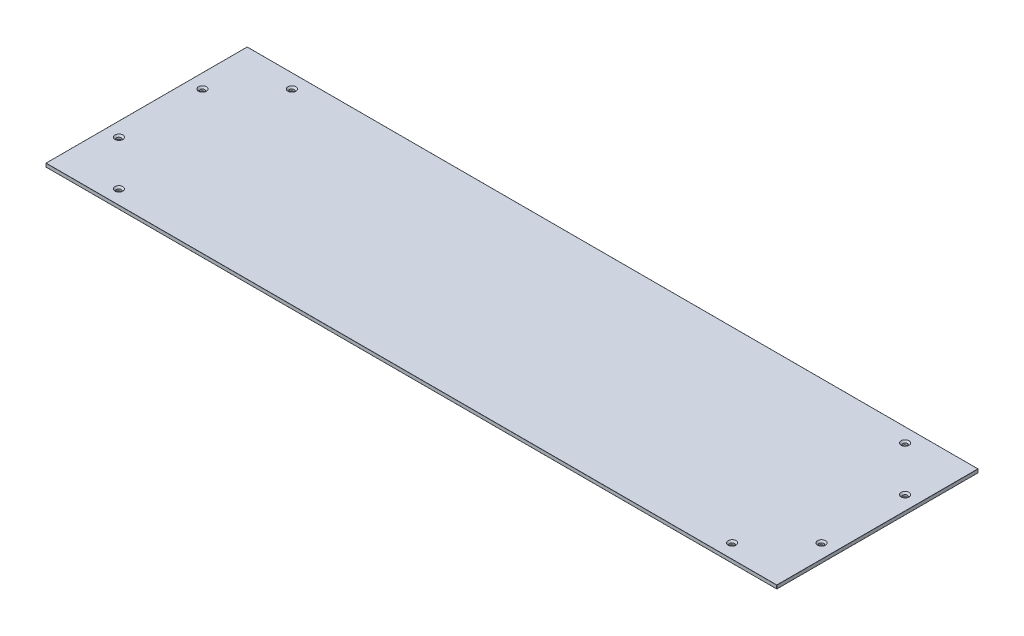
SolidWorks part; units mm, degrees
material "Glass"
ref_plane "Front Plane" through (0, 0, 0) normal (0, 0, 1) x (1, 0, 0)
ref_plane "Top Plane" through (0, 0, 0) normal (0, 1, 0) x (1, 0, 0)
ref_plane "Right Plane" through (0, 0, 0) normal (1, 0, 0) x (0, 0, -1)
sketch "Sketch1" plane through (0, 0, 0) normal (0, 1, 0) x (1, 0, 0)
  line L1 (-621, 171) -> (621, 171)
  line L2 (-621, 171) -> (-621, -171)
  line L3 (-621, -171) -> (621, -171)
  line L4 (621, 171) -> (621, -171)
  line L5 (-621, 171) -> (621, -171) construction
  line L6 (-621, -171) -> (621, 171) construction
  point P0 (0, 0)
  dimension "Largura" = 1242
  dimension "Profundidade" = 342
extrude "Boss-Extrude1" add sketch "Sketch1" along normal blind 6
sketch "Sketch2" plane through (0, 6, 0) normal (0, 1, 0) x (1, 0, 0)
  line L0 (-621, -171) -> (621, -171) construction
  line L1 (-621, 171) -> (-621, -171) construction
  line L2 (0, 171) -> (0, -171) construction
  line L3 (621, 171) -> (-621, 171) construction
  line L4 (-621, 0) -> (621, 0) construction
  line L5 (621, -171) -> (621, 171) construction
  circle A0 centre (-521, -147) radius 4
  circle A1 centre (521, -147) radius 4
  circle A2 centre (-597, -71) radius 4
  circle A3 centre (597, -71) radius 4
  circle A4 centre (597, 71) radius 4
  circle A5 centre (521, 147) radius 4
  circle A6 centre (-521, 147) radius 4
  circle A7 centre (-597, 71) radius 4
  dimension "D1" = 8
  dimension "D2" = 24
  dimension "D3" = 100
  dimension "D4" = 24
  dimension "D5" = 100
extrude "Cut-Extrude1" cut sketch "Sketch2" against normal through all
chamfer "Chamfer1" distance 2.75 angle 45 8 edges at (-521, 6, 151) (-597, 6, -75) (-521, 6, -151) (521, 6, -143) (597, 6, -67) (597, 6, 67) (521, 6, 143) (-597, 6, 75)
fillet "Fillet1" radius 0.2 12 edges at (621, 3, -171) (0, 0, -171) (0, 6, -171) (-621, 3, -171) (621, 0, 0) (621, 6, 0) (621, 3, 171) (-621, 0, 0) (-621, 6, 0) (-621, 3, 171) (0, 0, 171) (0, 6, 171)
